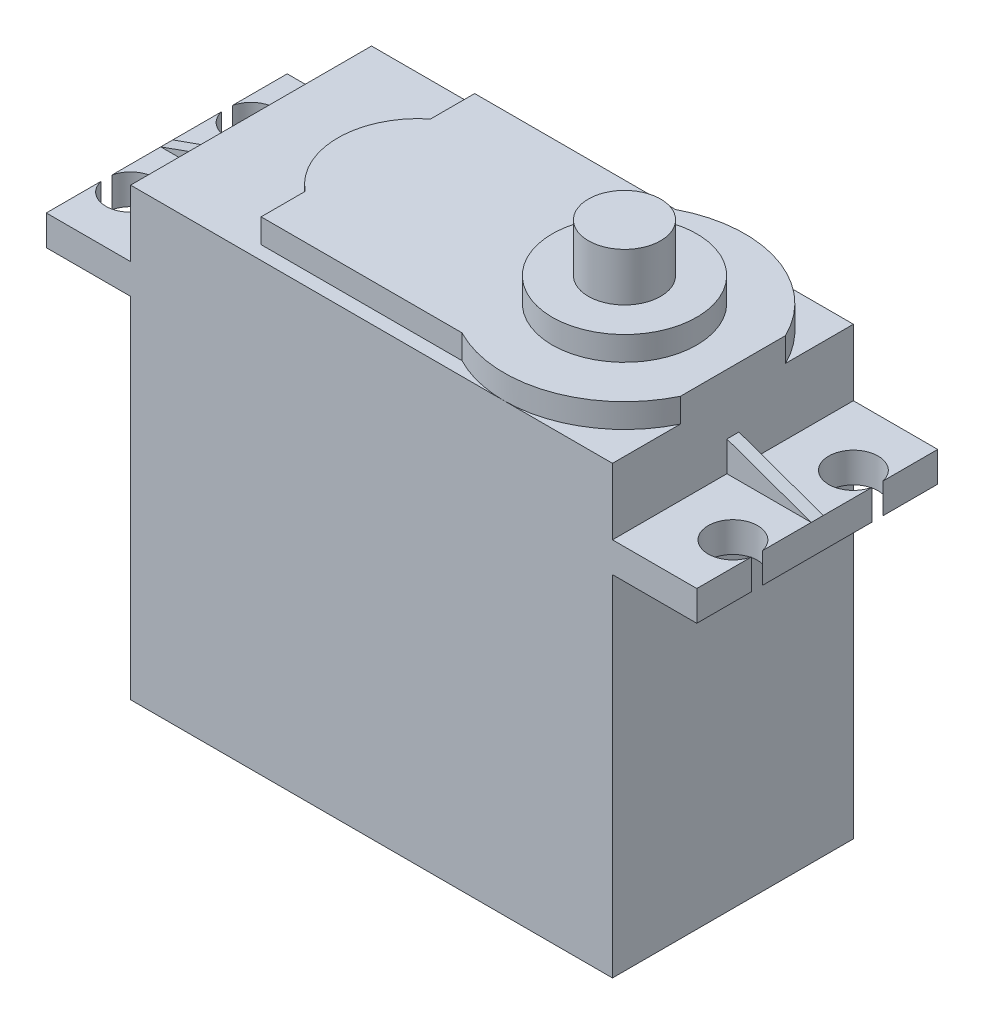
SolidWorks part; units mm, degrees
ref_plane "前视基准面" through (0, 0, 0) normal (0, 0, 1) x (1, 0, 0)
ref_plane "上视基准面" through (0, 0, 0) normal (0, 1, 0) x (1, 0, 0)
ref_plane "右视基准面" through (0, 0, 0) normal (1, 0, 0) x (0, 0, -1)
sketch "Sketch1" plane through (0, 0, 0) normal (0, 1, 0) x (1, 0, 0)
  line L1 (-20, -10) -> (20, -10)
  line L2 (-20, -10) -> (-20, 10)
  line L3 (-20, 10) -> (20, 10)
  line L4 (20, -10) -> (20, 10)
  line L5 (-20, -10) -> (20, 10) construction
  line L6 (-20, 10) -> (20, -10) construction
  point P0 (0, 0)
  dimension "D1" = 20
  dimension "D2" = 40
extrude "Boss-Extrude1" add sketch "Sketch1" along normal blind 29
sketch "Sketch2" plane through (0, 29, 0) normal (0, 1, 0) x (1, 0, 0)
  line L0 (20, 10) -> (-20, 10) construction
  line L1 (-27, -10) -> (27, -10)
  line L2 (-27, -10) -> (-27, 10)
  line L3 (-27, 10) -> (27, 10)
  line L4 (27, -10) -> (27, 10)
  line L5 (-27, -10) -> (27, 10) construction
  line L6 (-27, 10) -> (27, -10) construction
  point P0 (0, 0)
  dimension "D1" = 54
extrude "Boss-Extrude2" add sketch "Sketch2" along normal blind 2.5
sketch "Sketch3" plane through (0, 31.5, 0) normal (0, 1, 0) x (1, 0, 0)
  line L0 (27, 10) -> (-27, 10) construction
  line L1 (-20, -10) -> (20, -10)
  line L2 (-20, -10) -> (-20, 10)
  line L3 (-20, 10) -> (20, 10)
  line L4 (20, -10) -> (20, 10)
  line L5 (-20, -10) -> (20, 10) construction
  line L6 (-20, 10) -> (20, -10) construction
  point P0 (0, 0)
  dimension "D1" = 40
extrude "Boss-Extrude3" add sketch "Sketch3" along normal blind 5.5
sketch "Sketch4" plane through (0, 37, 0) normal (0, 1, 0) x (1, 0, 0)
  line L0 (27, -10) -> (27, 10) construction
  line L1 (-10.3029, 5.2039) -> (-10.3029, 8.8639)
  line L2 (-10.3029, -8.8639) -> (6.3705, -8.8639)
  line L3 (-10.3029, -8.8639) -> (-10.3029, -5.2039)
  line L4 (-10.3029, 8.8639) -> (6.3705, 8.8639)
  line L6 (20, -10) -> (20, 10) construction
  line L7 (20, -4.3589) -> (20, 4.3589)
  arc A0 (6.3705, -8.8639) -> (20, -4.3589) centre (11, 0) ccw
  arc A1 (-10.3029, 5.2039) -> (-10.3029, -5.2039) centre (-6.126, 0) ccw
  arc A2 (20, 4.3589) -> (6.3705, 8.8639) centre (11, 0) ccw
  point P4 (0, 0)
  dimension "D1" = 16
extrude "Boss-Extrude4" add sketch "Sketch4" along normal blind 2
sketch "Sketch5" plane through (0, 39, 0) normal (0, 1, 0) x (1, 0, 0)
  circle A0 centre (11, 0) radius 6
  dimension "D1" = 12
extrude "Boss-Extrude5" add sketch "Sketch5" along normal blind 2
sketch "Sketch6" plane through (0, 41, 0) normal (0, 1, 0) x (1, 0, 0)
  circle A0 centre (11, 0) radius 3
  dimension "D1" = 6
extrude "Boss-Extrude6" add sketch "Sketch6" along normal blind 4
sketch "Sketch7" plane through (0, 31.5, 0) normal (0, 1, 0) x (1, 0, 0)
  line L1 (-25, -5) -> (25, -5) construction
  line L2 (-25, -5) -> (-25, 5) construction
  line L3 (-25, 5) -> (25, 5) construction
  line L4 (25, -5) -> (25, 5) construction
  line L5 (-25, -5) -> (25, 5) construction
  line L6 (-25, 5) -> (25, -5) construction
  circle A0 centre (-25, 5) radius 2.05
  circle A1 centre (-25, -5) radius 2.05
  circle A2 centre (25, 5) radius 2.05
  circle A3 centre (25, -5) radius 2.05
  point P0 (0, 0)
  dimension "D1" = 4.1
  dimension "D2" = 50
  dimension "D3" = 10
extrude "Cut-Extrude2" cut sketch "Sketch7" against normal blind 4
ref_plane "Plane1" through (0, 0, 0) normal (0, 0, 1) x (1, 0, 0)
sketch "Sketch8" plane through (0, 0, 0) normal (0, 0, 1) x (1, 0, 0)
  line L0 (-20, 34) -> (-27, 31.5)
  line L1 (-20, 37) -> (-20, 31.5) construction
  line L2 (-27, 31.5) -> (-20, 31.5)
  line L3 (-20, 31.5) -> (-20, 34)
  line L4 (0, 0) -> (0, 37) construction
  line L5 (-20, 37) -> (11, 37) construction
  line L6 (20, 31.5) -> (20, 34)
  line L7 (27, 31.5) -> (20, 31.5)
  line L8 (20, 34) -> (27, 31.5)
  dimension "D1" = 2.5
extrude "Boss-Extrude8" add sketch "Sketch8" along normal blind 0.5 and the other way blind 0.5
